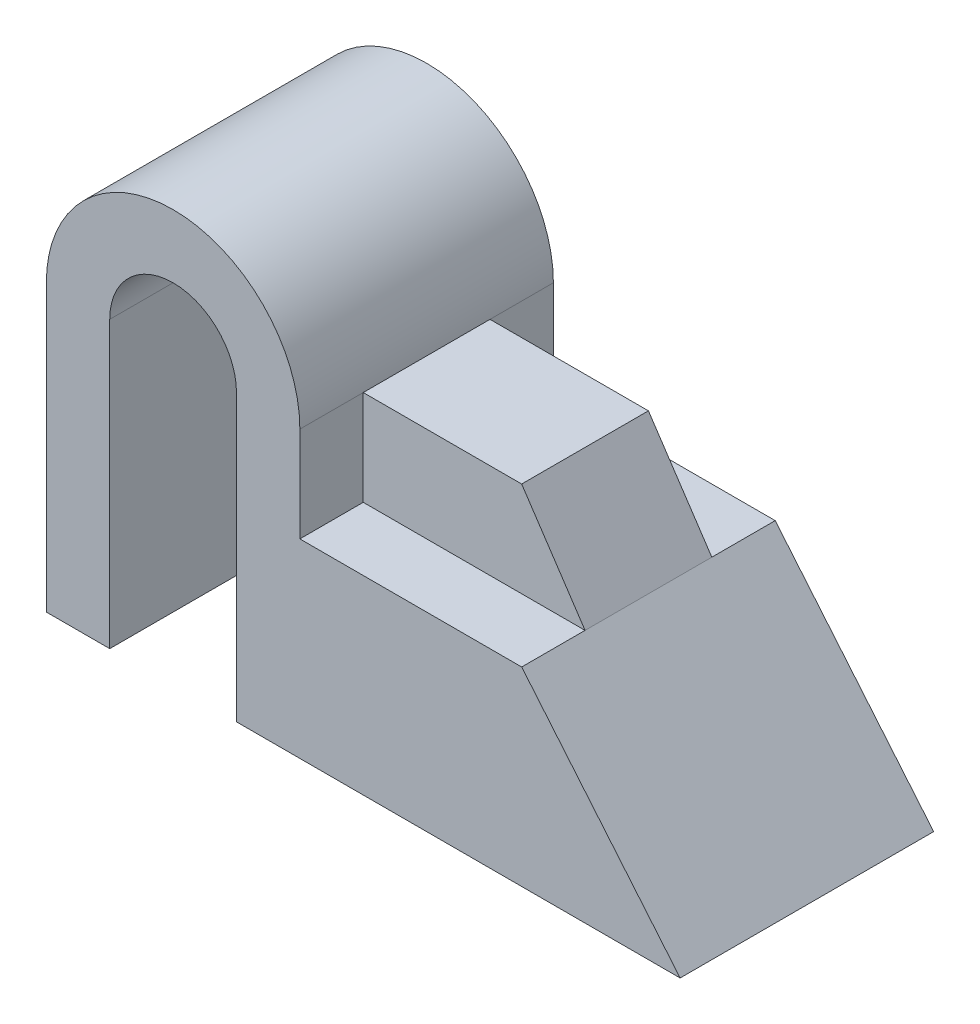
SolidWorks part; units mm, degrees
ref_plane "Front Plane" through (0, 0, 0) normal (0, 0, 1) x (1, 0, 0)
ref_plane "Top Plane" through (0, 0, 0) normal (0, 1, 0) x (1, 0, 0)
ref_plane "Right Plane" through (0, 0, 0) normal (1, 0, 0) x (0, 0, -1)
sketch "Sketch1" plane through (0, 0, 0) normal (0, 0, 1) x (1, 0, 0)
  line L3 (0, 0) -> (100, 0)
  line L4 (40, 30) -> (75, 30)
  line L5 (75, 30) -> (100, 0)
  line L6 (0, 45) -> (0, 0)
  line L8 (40, 45) -> (40, 30)
  arc A0 (0, 45) -> (20, 65) centre (20, 45) cw
  arc A1 (20, 65) -> (40, 45) centre (20, 45) cw
  point P1 (0, 0)
  dimension "D1" = 20
  dimension "D6" = 20
  dimension "D2" = 15
  dimension "D3" = 35
  dimension "D4" = 100
  dimension "D5" = 30
  dimension "D7" = 20
  dimension "D8" = 39.0512
  dimension "D9" = 20
extrude "Boss-Extrude1" add sketch "Sketch1" along normal mid plane 40
sketch "Sketch2" plane through (0, 0, 0) normal (0, 0, 1) x (1, 0, 0)
  line L0 (40, 30) -> (40, 45)
  line L1 (40, 30) -> (40, 45) construction
  line L2 (40, 45) -> (64.9958, 45)
  line L3 (64.9958, 45) -> (75, 30)
  line L4 (75, 30) -> (40, 30)
  dimension "D1" = 24.9958
  dimension "D2" = 18.0301
extrude "Boss-Extrude2" add sketch "Sketch2" along normal mid plane 20 contours L4 L0 L2 L3
sketch "Sketch3" plane through (0, 0, 0) normal (0, 0, 1) x (1, 0, 0)
  line L1 (0, 0) -> (100, 0) construction
  line L2 (10, 0) -> (10, 45)
  line L3 (10, 0) -> (30, 0)
  line L4 (30, 0) -> (30, 45)
  arc A0 (10, 45) -> (30, 45) centre (20, 45) cw
  point P0 (0, 0)
  dimension "D1" = 10
  dimension "D2" = 45
  dimension "D3" = 20
  dimension "D4" = 10
extrude "Cut-Extrude1" cut sketch "Sketch3" against normal mid plane 40 contours L3 L4 A0 L2
